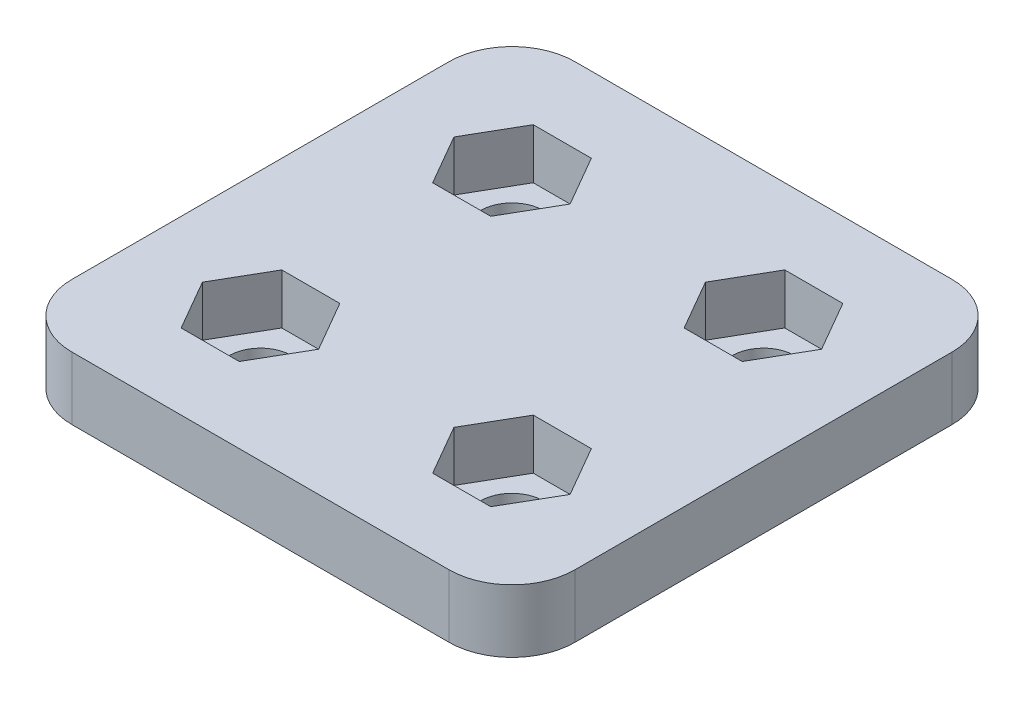
SolidWorks part; units mm, degrees
ref_plane "Front Plane" through (0, 0, 0) normal (0, 0, 1) x (1, 0, 0)
ref_plane "Top Plane" through (0, 0, 0) normal (0, 1, 0) x (1, 0, 0)
ref_plane "Right Plane" through (0, 0, 0) normal (1, 0, 0) x (0, 0, -1)
sketch "Sketch1" plane through (0, 0, 0) normal (0, 1, 0) x (1, 0, 0)
  line L1 (-20, -20) -> (20, -20)
  line L2 (-20, -20) -> (-20, 20)
  line L3 (-20, 20) -> (20, 20)
  line L4 (20, -20) -> (20, 20)
  line L5 (0, 20) -> (0, -20) construction
  line L6 (-20, 0) -> (20, 0) construction
  point P0 (0, 0)
  dimension "D1" = 40
  dimension "D2" = 40
extrude "Boss-Extrude1" add sketch "Sketch1" along normal blind 5
sketch "Sketch2" plane through (0, 5, 0) normal (0, 1, 0) x (1, 0, 0)
  line L1 (-10, -10) -> (10, -10)
  line L2 (-10, -10) -> (-10, 10)
  line L3 (-10, 10) -> (10, 10)
  line L4 (10, -10) -> (10, 10)
  line L5 (0, 10) -> (0, -10) construction
  line L6 (-10, 0) -> (10, 0) construction
  line L7 (-5.3812, 10) -> (-7.6906, 14)
  line L8 (-7.6906, 14) -> (-12.3094, 14)
  line L9 (-12.3094, 14) -> (-14.6188, 10)
  line L10 (-14.6188, 10) -> (-12.3094, 6)
  line L11 (-12.3094, 6) -> (-7.6906, 6)
  line L12 (-7.6906, 6) -> (-5.3812, 10)
  line L13 (14.6188, 10) -> (12.3094, 14)
  line L14 (12.3094, 14) -> (7.6906, 14)
  line L15 (7.6906, 14) -> (5.3812, 10)
  line L16 (5.3812, 10) -> (7.6906, 6)
  line L17 (7.6906, 6) -> (12.3094, 6)
  line L18 (12.3094, 6) -> (14.6188, 10)
  line L19 (-5.3812, -10) -> (-7.6906, -6)
  line L20 (-7.6906, -6) -> (-12.3094, -6)
  line L21 (-12.3094, -6) -> (-14.6188, -10)
  line L22 (-14.6188, -10) -> (-12.3094, -14)
  line L23 (-12.3094, -14) -> (-7.6906, -14)
  line L24 (-7.6906, -14) -> (-5.3812, -10)
  line L25 (14.6188, -10) -> (12.3094, -6)
  line L26 (12.3094, -6) -> (7.6906, -6)
  line L27 (7.6906, -6) -> (5.3812, -10)
  line L28 (5.3812, -10) -> (7.6906, -14)
  line L29 (7.6906, -14) -> (12.3094, -14)
  line L30 (12.3094, -14) -> (14.6188, -10)
  circle A4 centre (-10, 10) radius 4 construction
  circle A5 centre (10, 10) radius 4 construction
  circle A6 centre (-10, -10) radius 4 construction
  circle A7 centre (10, -10) radius 4 construction
  point P0 (0, 0)
  dimension "D3" = 8
  dimension "D1" = 20
  dimension "D2" = 20
extrude "Cut-Extrude1" cut sketch "Sketch2" against normal blind 4
sketch "Sketch3" plane through (0, 1, 0) normal (0, 1, 0) x (1, 0, 0)
  circle A0 centre (-10, 10) radius 2.5
  circle A1 centre (10, 10) radius 2.5
  circle A2 centre (-10, -10) radius 2.5
  circle A3 centre (10, -10) radius 2.5
  point P12 (0, 0)
  point P13 (0, 0)
  point P14 (0, 0)
  point P15 (0, 0)
  point P16 (0, 0)
  dimension "D1" = 5
extrude "Cut-Extrude2" cut sketch "Sketch3" against normal through all
fillet "Fillet1" radius 5 4 edges at (-20, 2.5, 20) (20, 2.5, 20) (20, 2.5, -20) (-20, 2.5, -20)
